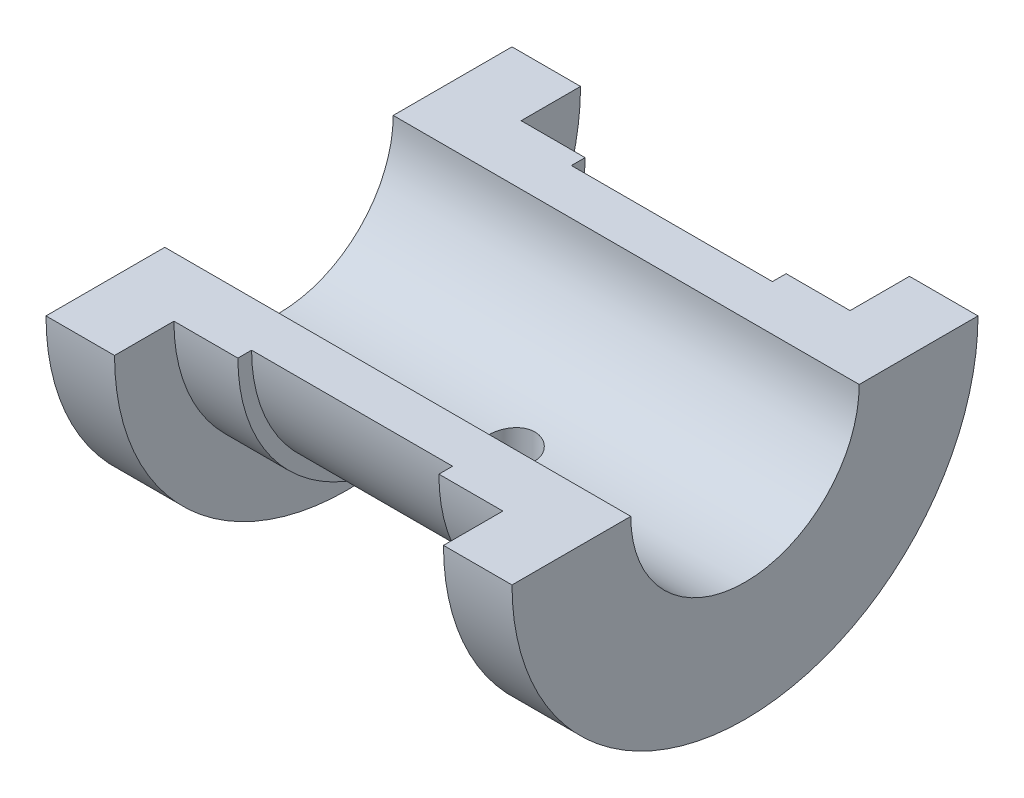
SolidWorks part; units mm, degrees
ref_plane "Front Plane" through (0, 0, 0) normal (0, 0, 1) x (1, 0, 0)
ref_plane "Top Plane" through (0, 0, 0) normal (0, 1, 0) x (1, 0, 0)
ref_plane "Right Plane" through (0, 0, 0) normal (1, 0, 0) x (0, 0, -1)
sketch "Sketch2" plane through (0, 0, 0) normal (0, 1, 0) x (1, 0, 0)
  line L0 (0, 0) -> (0, 66.6493) construction
  line L1 (25.5, 0) -> (-25.5, 0)
  line L2 (-25.5, 0) -> (-25.5, 25.5)
  line L3 (-18, 25.5) -> (-18, 19)
  line L4 (-18, 19) -> (-11, 19)
  line L5 (-11, 19) -> (-11, 17.5)
  line L6 (-11, 17.5) -> (11, 17.5)
  line L7 (-25.5, 25.5) -> (-18, 25.5)
  line L8 (25.5, 25.5) -> (18, 25.5)
  line L9 (11, 19) -> (11, 17.5)
  line L10 (18, 19) -> (11, 19)
  line L11 (18, 25.5) -> (18, 19)
  line L12 (25.5, 0) -> (25.5, 25.5)
  point P13 (0, 17.5)
  dimension "D1" = 51
  dimension "D2" = 22
  dimension "D3" = 36
  dimension "D4" = 25.5
  dimension "D5" = 19
  dimension "D6" = 17.5
revolve "Revolve3" add sketch "Sketch2" angle 180 about L1
sketch "Sketch3" plane through (-25.5, 0, 0) normal (-1, 0, 0) x (0, 0, 1)
  line L0 (25.5, 0) -> (-25.5, 0) construction
  line L1 (12.5, 0) -> (-12.5, 0)
  arc A0 (-12.5, 0) -> (12.5, 0) centre (0, 0) ccw
  dimension "D1" = 25
extrude "Cut-Extrude1" cut sketch "Sketch3" against normal through all contours A0 L1
hole_wizard "Ø6.0 (6) Diameter Hole1" positions "3DSketch3" profile "Sketch8" hole size "Ø6.0" standard "ANSI Metric" end condition through all
sketch3d "3DSketch3"
  point P0 (0, -17.5, 0)
  dimension "D1" = 0
  dimension "D2" = 0
sketch "Sketch8" plane through (0, -17.5, 0) normal (1, 0, 0) x (0, 0, -1)
  line L0 (0, 0) -> (0, 17.5)
  line L1 (0, 17.5) -> (2.5, 17.5)
  line L2 (2.5, 17.5) -> (2.5, 0)
  line L5 (2.5, 0) -> (0, 0)
  line L11 (0, -6.35) -> (0, 107.95) construction
  dimension "Thru Hole Dia." = 5
  dimension "Thru Hole Depth" = 17.5
